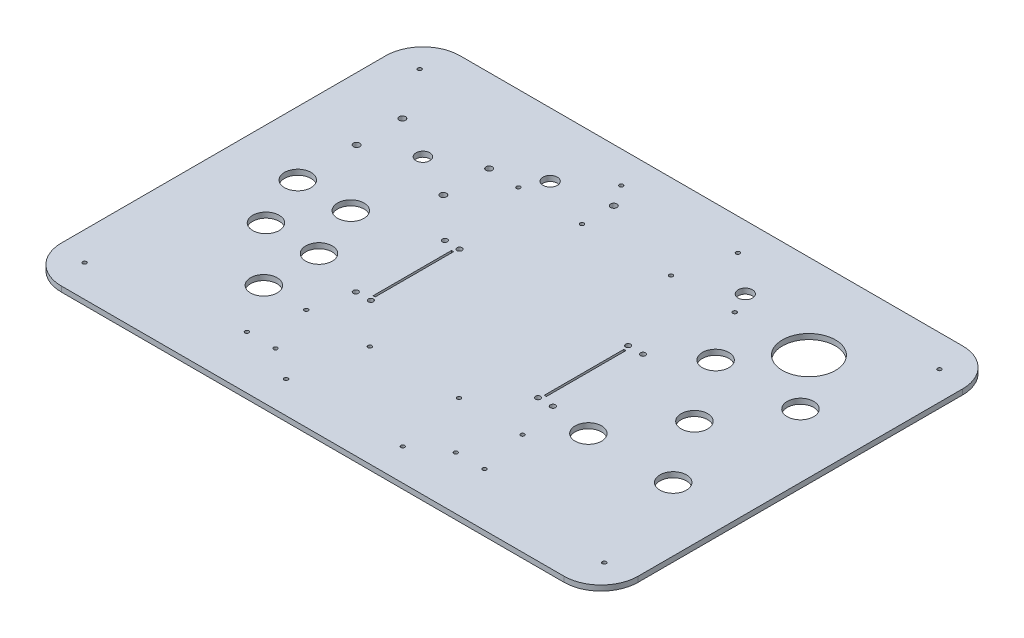
SolidWorks part; units mm, degrees
material "Perspex (TM) GS Acrylic Cast Sheet"
ref_plane "Front Plane" through (0, 0, 0) normal (0, 0, 1) x (1, 0, 0)
ref_plane "Top Plane" through (0, 0, 0) normal (0, 1, 0) x (1, 0, 0)
ref_plane "Right Plane" through (0, 0, 0) normal (1, 0, 0) x (0, 0, -1)
sketch "Sketch1" plane through (0, 0, 0) normal (0, 1, 0) x (1, 0, 0)
  line L1 (0, 0) -> (544, 0)
  line L2 (0, 0) -> (0, 376)
  line L3 (0, 376) -> (544, 376)
  line L4 (544, 0) -> (544, 376)
  dimension "D1" = 544
  dimension "D2" = 376
extrude "Boss-Extrude1" add sketch "Sketch1" along normal blind 5
sketch "Sketch2" plane through (0, 5, 0) normal (0, 1, 0) x (1, 0, 0)
  line L0 (544, 376) -> (0, 376) construction
  line L1 (100, 276) -> (165.8433, 276) construction
  line L2 (100, 276) -> (100, 296.2555) construction
  line L3 (0, 376) -> (0, 0) construction
  circle A0 centre (100, 276) radius 6.5
  circle A2 centre (140.91, 297.59) radius 3
  circle A3 centre (140.91, 254.41) radius 3
  circle A4 centre (59.09, 254.41) radius 3
  circle A5 centre (59.09, 297.59) radius 3
  dimension "D1" = 13
  dimension "D2" = 100
  dimension "D5" = 6
  dimension "D3" = 40.91
  dimension "D4" = 21.59
  dimension "D6" = 100
extrude "1 Joyystick" cut sketch "Sketch2" against normal through all
sketch "Sketch3" plane through (0, 5, 0) normal (0, 1, 0) x (1, 0, 0)
  line L0 (0, 376) -> (0, 0) construction
  line L2 (512, 378) -> (32, 378) construction
  circle A0 centre (60, 198) radius 12.5
  circle A1 centre (110, 198) radius 12.5
  circle A2 centre (80, 148) radius 12.5
  circle A3 centre (130, 148) radius 12.5
  circle A4 centre (130, 96) radius 12.5
  dimension "D1" = 25
  dimension "D2" = 25
  dimension "D3" = 25
  dimension "D4" = 25
  dimension "D5" = 25
  dimension "D11" = 180
  dimension "D6" = 60
  dimension "D7" = 50
  dimension "D8" = 50
  dimension "D9" = 50
  dimension "D10" = 52
  dimension "D12" = 20
extrude "1 Buttons" cut sketch "Sketch3" against normal through all
sketch "Sketch4" plane through (0, 5, 0) normal (0, 1, 0) x (1, 0, 0)
  line L0 (544, 376) -> (0, 376) construction
  line L1 (0, 376) -> (0, 0) construction
  circle A0 centre (180, 316) radius 6.75
  dimension "D1" = 13.5
  dimension "D2" = 60
  dimension "D3" = 180
extrude "1 Rocket Switch" cut sketch "Sketch4" against normal through all
sketch "Sketch5" plane through (0, 5, 0) normal (0, 1, 0) x (1, 0, 0)
  line L0 (192, 176) -> (210.2533, 176) construction
  line L1 (190, 213) -> (192, 213)
  line L2 (190, 213) -> (190, 139)
  line L3 (190, 139) -> (192, 139)
  line L4 (192, 213) -> (192, 139)
  line L5 (190, 176) -> (192, 176) construction
  line L7 (544, 376) -> (0, 376) construction
  line L8 (185.3835, 194.2678) -> (184.0453, 100.019) construction
  line L9 (0, 376) -> (0, 0) construction
  circle A0 centre (178.7197, 218) radius 2.4
  circle A1 centre (192.7183, 217.8012) radius 2.4
  circle A2 centre (192.7183, 134.1988) radius 2.4
  circle A3 centre (178.7197, 134) radius 2.4
  point P7 (191, 213)
  dimension "D5" = 4.8
  dimension "D1" = 2
  dimension "D2" = 74
  dimension "D3" = 5.35
  dimension "D4" = 190
  dimension "D6" = 7
  dimension "D7" = 200
  dimension "D8" = 5
  dimension "D9" = 4.8012
extrude "1 Potentiometer" cut sketch "Sketch5" against normal through all
fillet "Fillet1" radius 35 4 edges at (0, 2.5, 0) (544, 2.5, 0) (544, 2.5, -376) (0, 2.5, -376)
sketch "Sketch6" plane through (0, 5, 0) normal (0, 1, 0) x (1, 0, 0)
  line L0 (544, 35) -> (544, 341) construction
  line L2 (544, 188) -> (0, 188) construction
  line L3 (0, 341) -> (0, 35) construction
  circle A0 centre (484, 248) radius 12.5
  circle A1 centre (404, 248) radius 12.5
  circle A2 centre (484, 128) radius 12.5
  circle A3 centre (404, 128) radius 12.5
  circle A4 centre (444, 188) radius 12.5
  dimension "D1" = 25
  dimension "D2" = 25
  dimension "D3" = 25
  dimension "D4" = 25
  dimension "D5" = 25
  dimension "D6" = 80
  dimension "D7" = 60
  dimension "D8" = 80
  dimension "D9" = 120
  dimension "D10" = 60
  dimension "D11" = 60
  dimension "D12" = 40
extrude "2 Buttons" cut sketch "Sketch6" against normal through all
sketch "Sketch8" plane through (0, 5, 0) normal (0, 1, 0) x (1, 0, 0)
  line L0 (353, 213.5) -> (353, 138.5) construction
  line L1 (354, 213.5) -> (352, 213.5)
  line L2 (354, 213.5) -> (354, 138.5)
  line L3 (354, 138.5) -> (352, 138.5)
  line L4 (352, 213.5) -> (352, 138.5)
  line L5 (358, 205.9826) -> (358, 86.9169) construction
  line L6 (354, 176) -> (327.2352, 176) construction
  line L8 (544, 35) -> (544, 341) construction
  line L9 (509, 376) -> (35, 376) construction
  circle A0 centre (365, 218.5) radius 2.4
  circle A1 centre (365, 133.5) radius 2.4
  circle A2 centre (351, 133.5) radius 2.4
  circle A3 centre (351, 218.5) radius 2.4
  point P22 (353, 176)
  dimension "D2" = 4.8
  dimension "D3" = 42.5
  dimension "D1" = 5
  dimension "D4" = 1
  dimension "D5" = 2
  dimension "D6" = 190
  dimension "D7" = 200
  dimension "D8" = 7
sketch "Sketch9" plane through (0, 5, 0) normal (0, 1, 0) x (1, 0, 0)
  line L0 (544, 35) -> (544, 341) construction
  line L1 (509, 376) -> (35, 376) construction
  circle A0 centre (444, 296) radius 25
  dimension "D1" = 50
  dimension "D2" = 100
  dimension "D3" = 80
extrude "2 speaker" cut sketch "Sketch9" against normal through all
sketch "Sketch10" plane through (0, 5, 0) normal (0, 1, 0) x (1, 0, 0)
  line L0 (509, 376) -> (35, 376) construction
  line L1 (544, 35) -> (544, 341) construction
  circle A0 centre (364, 316) radius 6.75
  dimension "D1" = 13.5
  dimension "D2" = 60
  dimension "D3" = 180
extrude "2 Potentiometer" cut sketch "Sketch8" against normal through all
sketch "Sketch11" plane through (0, 5, 0) normal (0, 1, 0) x (1, 0, 0)
  line L0 (314, 96) -> (314, 294.2) construction
  line L1 (374, 96) -> (374, 296) construction
  line L2 (365.4787, 96) -> (281.3845, 96) construction
  line L3 (356.6021, 296) -> (314, 296) construction
  line L4 (544, 35) -> (544, 341) construction
  line L5 (509, 376) -> (35, 376) construction
  circle A0 centre (374, 96) radius 1.8
  circle A1 centre (314, 96) radius 1.8
  circle A2 centre (314, 296) radius 1.8
  circle A3 centre (374, 296) radius 1.8
  dimension "D1" = 200
  dimension "D3" = 3.6
  dimension "D4" = 3.6
  dimension "D5" = 3.6
  dimension "D6" = 3.6
  dimension "D2" = 60
  dimension "D7" = 170
  dimension "D8" = 80
extrude "2 PCB1" cut sketch "Sketch11" against normal through all
sketch "Sketch12" plane through (0, 5, 0) normal (0, 1, 0) x (1, 0, 0)
  line L0 (159.4963, 96) -> (271.8437, 96) construction
  line L1 (244.3419, 296) -> (170, 296) construction
  line L2 (230, 96) -> (230, 296) construction
  line L3 (170, 30.2464) -> (170, 266.6202) construction
  line L5 (509, 376) -> (35, 376) construction
  line L6 (0, 341) -> (0, 35) construction
  circle A0 centre (230, 96) radius 1.8
  circle A1 centre (170, 96) radius 1.8
  circle A2 centre (230, 296) radius 1.8
  circle A3 centre (170, 296) radius 1.8
  dimension "D3" = 3.6
  dimension "D4" = 3.6
  dimension "D7" = 3.6
  dimension "D8" = 3.6
  dimension "D1" = 200
  dimension "D2" = 60
  dimension "D5" = 170
  dimension "D6" = 80
extrude "1 PCB2" cut sketch "Sketch12" against normal through all
sketch "Sketch13" plane through (0, 5, 0) normal (0, 1, 0) x (1, 0, 0)
  line L1 (544, 35) -> (544, 341) construction
  line L2 (35, 0) -> (509, 0) construction
  circle A0 centre (384, 50) radius 1.8
  circle A1 centre (357, 50) radius 1.8
  dimension "D1" = 3.6
  dimension "D2" = 3.6
  dimension "D3" = 27
  dimension "D4" = 50
  dimension "D5" = 160
extrude "2 USB Connector" cut sketch "Sketch13" against normal through all
sketch "Sketch14" plane through (0, 5, 0) normal (0, 1, 0) x (1, 0, 0)
  line L1 (0, 341) -> (0, 35) construction
  line L2 (35, 0) -> (509, 0) construction
  circle A0 centre (187, 50) radius 1.8
  circle A1 centre (160, 50) radius 1.8
  dimension "D1" = 3.6
  dimension "D2" = 3.6
  dimension "D4" = 50
  dimension "D3" = 27
  dimension "D5" = 160
extrude "1 USB Connector" cut sketch "Sketch14" against normal through all
sketch "Sketch15" plane through (0, 5, 0) normal (0, 1, 0) x (1, 0, 0)
  line L0 (509, 376) -> (35, 376) construction
  line L1 (0, 341) -> (0, 35) construction
  circle A0 centre (230, 326) radius 3
  dimension "D1" = 6
  dimension "D2" = 50
  dimension "D3" = 230
extrude "Power" cut sketch "Sketch15" against normal through all
sketch "Sketch16" plane through (0, 5, 0) normal (0, 1, 0) x (1, 0, 0)
  line L0 (544, 35) -> (544, 341) construction
  line L1 (35, 0) -> (509, 0) construction
  line L2 (272, 0) -> (272, 376) construction
  line L3 (509, 376) -> (35, 376) construction
  circle A0 centre (517, 30) radius 1.8
  circle A1 centre (327, 30) radius 1.8
  circle A2 centre (517, 346) radius 1.8
  circle A3 centre (327, 346) radius 1.8
  circle A4 centre (217, 346) radius 1.8
  circle A5 centre (27, 346) radius 1.8
  circle A6 centre (217, 30) radius 1.8
  circle A7 centre (27, 30) radius 1.8
  dimension "D1" = 27
  dimension "D3" = 3.6
  dimension "D5" = 3.6
  dimension "D8" = 3.6
  dimension "D9" = 3.6
  dimension "D2" = 30
  dimension "D4" = 190
  dimension "D6" = 316
  dimension "D7" = 316
extrude "LED fixings" cut sketch "Sketch16" against normal through all
extrude "Cut-Extrude1" cut sketch "Sketch10" against normal through all
